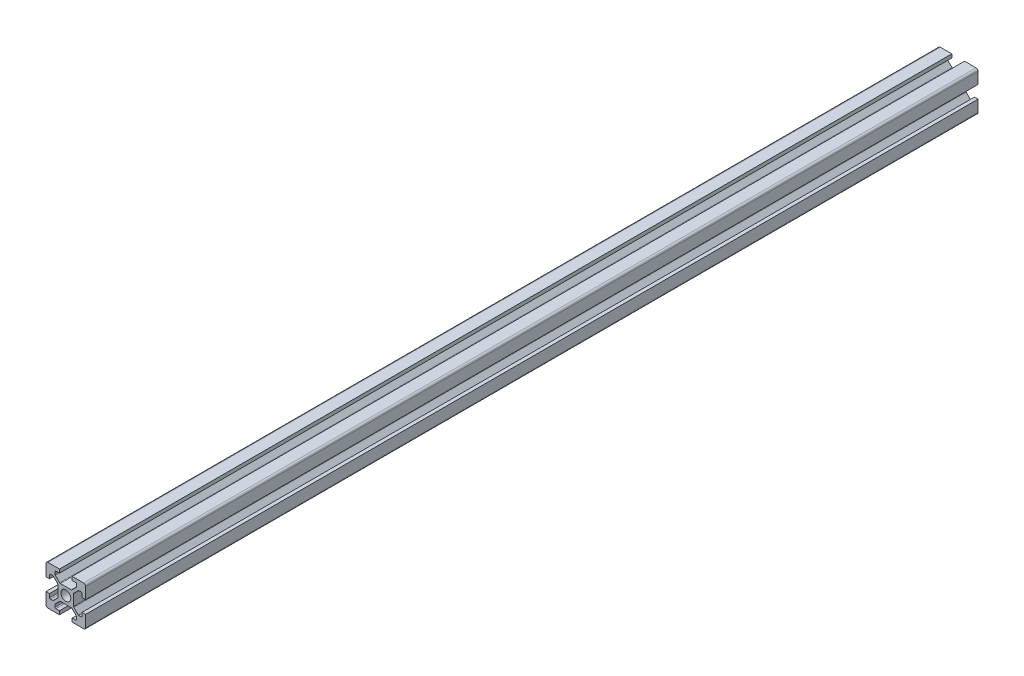
SolidWorks part; units mm, degrees
material "1060 Alloy"
ref_plane "Front Plane" through (0, 0, 0) normal (0, 0, 1) x (1, 0, 0)
ref_plane "Top Plane" through (0, 0, 0) normal (0, 1, 0) x (1, 0, 0)
ref_plane "Right Plane" through (0, 0, 0) normal (1, 0, 0) x (0, 0, -1)
sketch "Sketch1" plane through (0, 0, 0) normal (0, 0, 1) x (1, 0, 0)
  line L0 (20, 0) -> (-8.059, 28.059) construction
  line L1 (0, 0) -> (6.8, 0)
  line L2 (0, 0) -> (0, 6.8)
  line L3 (0, 20) -> (6.8, 20)
  line L4 (20, 0) -> (20, 6.8)
  line L5 (6.8, 20) -> (6.8, 18.2)
  line L6 (20, 20) -> (8.2322, 8.2322) construction
  line L7 (12.95, 6.1) -> (7.05, 6.1)
  line L8 (13.9, 7.05) -> (13.9, 12.95)
  line L9 (12.95, 13.9) -> (7.05, 13.9)
  line L10 (6.1, 7.05) -> (6.1, 12.95)
  line L11 (13.9, 6.1) -> (6.1, 13.9) construction
  line L12 (13.9, 13.9) -> (6.1, 6.1) construction
  line L13 (4.55, 16.4) -> (7.05, 13.9)
  line L14 (13.2, 18.2) -> (13.2, 20)
  line L15 (1.8, 6.8) -> (0, 6.8)
  line L16 (0, 13.2) -> (0, 20)
  line L17 (0, 13.2) -> (1.8, 13.2)
  line L18 (10, 10) -> (10, 13.9) construction
  line L19 (16.4, 4.55) -> (13.9, 7.05)
  line L20 (4.55, 16.4) -> (4.55, 18.2)
  line L21 (4.55, 18.2) -> (6.8, 18.2)
  line L22 (13.2, 18.2) -> (15.45, 18.2)
  line L23 (15.45, 18.2) -> (15.45, 16.4)
  line L24 (15.45, 16.4) -> (12.95, 13.9)
  line L25 (16.4, 4.55) -> (18.2, 4.55)
  line L26 (18.2, 4.55) -> (18.2, 6.8)
  line L27 (20, 6.8) -> (18.2, 6.8)
  line L28 (18.2, 13.2) -> (20, 13.2)
  line L29 (18.2, 13.2) -> (18.2, 15.45)
  line L30 (18.2, 15.45) -> (16.4, 15.45)
  line L31 (16.4, 15.45) -> (13.9, 12.95)
  line L32 (1.8, 4.55) -> (3.6, 4.55)
  line L33 (3.6, 15.45) -> (6.1, 12.95)
  line L34 (3.6, 15.45) -> (1.8, 15.45)
  line L35 (1.8, 15.45) -> (1.8, 13.2)
  line L36 (0, 13.2) -> (1.8, 13.2)
  line L37 (1.8, 6.8) -> (0, 6.8)
  line L38 (3.6, 4.55) -> (6.1, 7.05)
  line L39 (1.8, 6.8) -> (1.8, 4.55)
  line L40 (15.45, 3.6) -> (12.95, 6.1)
  line L41 (4.55, 3.6) -> (7.05, 6.1)
  line L42 (4.55, 1.8) -> (4.55, 3.6)
  line L43 (6.8, 1.8) -> (4.55, 1.8)
  line L44 (6.8, 1.8) -> (6.8, 0)
  line L45 (15.45, 3.6) -> (15.45, 1.8)
  line L46 (15.45, 1.8) -> (13.2, 1.8)
  line L47 (13.2, 0) -> (13.2, 1.8)
  line L48 (13.2, 20) -> (20, 20)
  line L49 (20, 13.2) -> (20, 20)
  line L50 (13.2, 0) -> (20, 0)
  line L51 (6.1, 6.1) -> (-5.5045, -5.5045) construction
  circle A0 centre (10, 10) radius 2.5
  point P25 (10, 16.4)
  point P39 (13.2, 19.1)
  point P46 (0.9, 6.8)
  dimension "D3" = 5
  dimension "D2" = 20
  dimension "D4" = 7.8
  dimension "D5" = 7.8
  dimension "D6" = 6.8
  dimension "D7" = 6.8
  dimension "D8" = 1.8
  dimension "D9" = 10.9
  dimension "D10" = 1.8
  dimension "D11" = 10.9
  dimension "D12" = 20
extrude "Boss-Extrude1" add sketch "Sketch1" along normal blind 450 contours L47 L50 L4 L27 L26 L25 L19 L8 L31 L30 L29 L28 L49 L48 L14 L22 L23 L24 L9 L13 L20 L21 L5 L3 L16 L17 L35 L34 L33 L10 L38 L32 L39 L15 L2 L1 L44 L43 L42 L41 L7 L40 L45 L46 A0
fillet "Fillet1" radius 1 4 edges at (20, 20, 225) (20, 0, 225) (0, 0, 225) (0, 20, 225)
fillet "Fillet2" radius 0.5 6 edges at (4.55, 18.2, 225) (4.55, 16.4, 225) (7.05, 13.9, 225) (15.45, 18.2, 225) (15.45, 16.4, 225) (12.95, 13.9, 225)
fillet "Fillet3" radius 0.5 6 edges at (18.2, 15.45, 225) (16.4, 15.45, 225) (13.9, 12.95, 225) (18.2, 4.55, 225) (13.9, 7.05, 225) (16.4, 4.55, 225)
fillet "Fillet4" radius 0.5 6 edges at (1.8, 15.45, 225) (3.6, 15.45, 225) (6.1, 12.95, 225) (3.6, 4.55, 225) (1.8, 4.55, 225) (6.1, 7.05, 225)
fillet "Fillet5" radius 0.5 6 edges at (7.05, 6.1, 225) (4.55, 3.6, 225) (4.55, 1.8, 225) (15.45, 1.8, 225) (15.45, 3.6, 225) (12.95, 6.1, 225)
